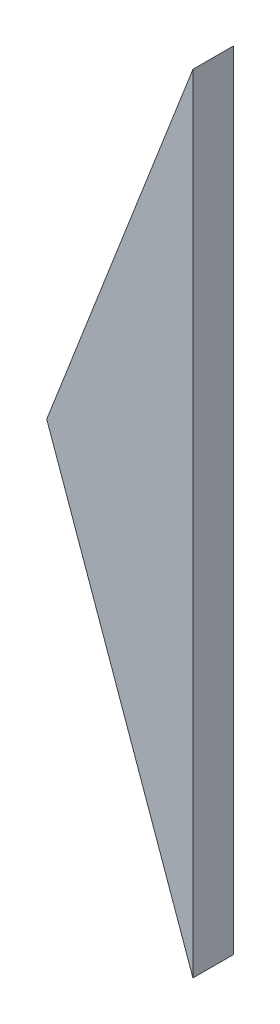
SolidWorks part; units mm, degrees
ref_plane "Plan de face" through (0, 0, 0) normal (0, 0, 1) x (1, 0, 0)
ref_plane "Plan de dessus" through (0, 0, 0) normal (0, 1, 0) x (1, 0, 0)
ref_plane "Plan de droite" through (0, 0, 0) normal (1, 0, 0) x (0, 0, -1)
sketch "Esquisse1" plane through (0, 0, 0) normal (0, 0, 1) x (1, 0, 0)
  line L0 (-25.7431, -66.2226) -> (-14.8734, -38.261)
  line L1 (-14.8734, -38.261) -> (-14.8734, -96.7699)
  line L2 (-14.8734, -96.7699) -> (-25.7431, -66.2226)
  line L3 (0, 0) -> (-26.1476, -67.2634) construction
  line L4 (2.5315, -145.6832) -> (-26.1174, -65.1707) construction
  dimension "D1" = 30
extrude "Boss.-Extru.1" add sketch "Esquisse1" against normal blind 3
